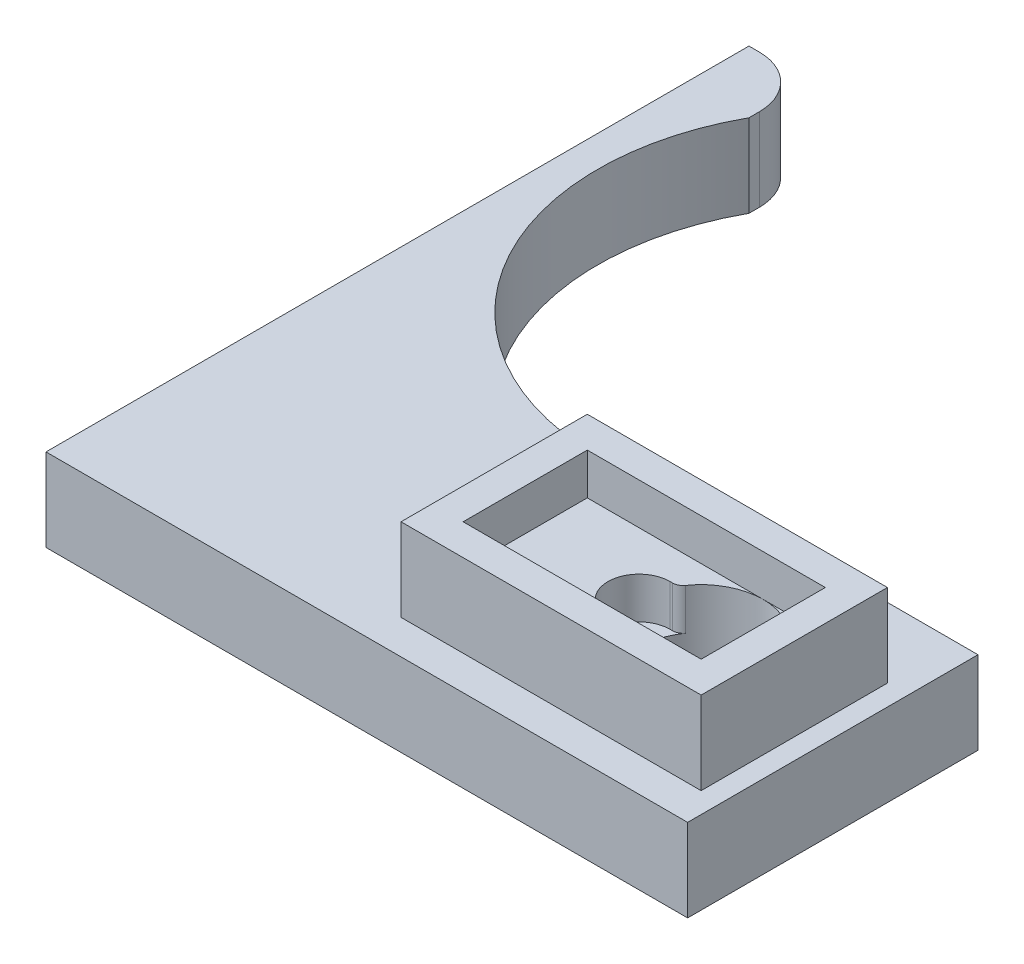
SolidWorks part; units mm, degrees
ref_plane "Plan de face" through (0, 0, 0) normal (0, 0, 1) x (1, 0, 0)
ref_plane "Plan de dessus" through (0, 0, 0) normal (0, 1, 0) x (1, 0, 0)
ref_plane "Plan de droite" through (0, 0, 0) normal (1, 0, 0) x (0, 0, -1)
sketch "Esquisse1" plane through (0, 0, 0) normal (0, 1, 0) x (1, 0, 0)
  line L1 (0, 0) -> (6, 0)
  line L2 (0, 0) -> (0, 67.9235)
  line L3 (0, 67.9235) -> (1, 67.9235)
  line L4 (6, 0) -> (6, 67.9235) construction
  line L5 (36, 0) -> (6, 0)
  line L6 (6, 61.9235) -> (6, 62.9235)
  line L7 (52, 50.3046) -> (52, 0) construction
  line L8 (36, 28.056) -> (62, 28.056)
  line L10 (36, 0) -> (62, 0)
  line L11 (62, 28.056) -> (62, 0)
  line L12 (36, 28.056) -> (36, 0) construction
  line L13 (52, 12.3046) -> (51, 12.3046) construction
  arc A0 (6, 61.9235) -> (36, 28.056) centre (27, 50.3046) ccw
  circle A1 centre (27, 50.3046) radius 25 construction
  arc A2 (1, 67.9235) -> (6, 62.9235) centre (1, 62.9235) cw
  circle A3 centre (51, 12.3046) radius 6
  dimension "D1" = 24
  dimension "D3" = 50
  dimension "D7" = 5
  dimension "D9" = 12
  dimension "D2" = 21
  dimension "D4" = 30
  dimension "D5" = 6
  dimension "D6" = 6
  dimension "D8" = 1
  dimension "D10" = 38
  dimension "D11" = 62
extrude "Boss.-Extru.1" add sketch "Esquisse1" along normal blind 8
sketch "Esquisse2" plane through (0, 8, 0) normal (0, 1, 0) x (1, 0, 0)
  line L0 (51, 12.3046) -> (45, 12.3046) construction
  line L1 (45, 15.3046) -> (45.2554, 15.3046)
  line L2 (45, 9.3046) -> (45.2554, 9.3046)
  line L8 (31, 21.3046) -> (60, 21.3046)
  line L9 (31, 21.3046) -> (31, 3.3046)
  line L10 (31, 3.3046) -> (60, 3.3046)
  line L11 (60, 21.3046) -> (60, 3.3046)
  circle A0 centre (51, 12.3046) radius 6 construction
  circle A1 centre (45, 12.3046) radius 3 construction
  arc A2 (46.0761, 15.7332) -> (46.0761, 8.876) centre (51, 12.3046) cw
  arc A3 (45, 15.3046) -> (45, 9.3046) centre (45, 12.3046) ccw
  arc A4 (45.2554, 9.3046) -> (46.0761, 8.876) centre (45.2554, 8.3046) cw
  arc A5 (45.2554, 15.3046) -> (46.0761, 15.7332) centre (45.2554, 16.3046) ccw
  point P15 (45.8038, 9.3046)
  point P18 (45.8038, 15.3046)
  point P27 (60, 12.3046)
  dimension "D1" = 12
  dimension "D2" = 6
  dimension "D4" = 1
  dimension "D3" = 6
  dimension "D5" = 9
  dimension "D7" = 18
  dimension "D8" = 29
extrude "Boss.-Extru.2" add sketch "Esquisse2" along normal blind 4 contours L9 L8 L11 L10 | A3 L2 A4 A2 A5 L1
sketch "Esquisse3" plane through (0, 12, 0) normal (0, 1, 0) x (1, 0, 0)
  line L1 (34, 18.3046) -> (57, 18.3046)
  line L2 (34, 18.3046) -> (34, 6.3046)
  line L3 (34, 6.3046) -> (57, 6.3046)
  line L4 (57, 18.3046) -> (57, 6.3046)
  line L5 (31, 21.3046) -> (60, 21.3046)
  line L6 (31, 21.3046) -> (31, 3.3046)
  line L7 (31, 3.3046) -> (60, 3.3046)
  line L8 (60, 21.3046) -> (60, 3.3046)
  arc A0 (46.0761, 8.876) -> (46.0761, 15.7332) centre (51, 12.3046) ccw construction
  dimension "D1" = 12
  dimension "D2" = 23
extrude "Boss.-Extru.3" add sketch "Esquisse3" along normal blind 4
sketch "Esquisse4" plane through (0, 0, 0) normal (0, -1, 0) x (1, 0, 0)
  line L0 (62, -28.056) -> (36, -28.056) construction
  line L1 (47.7, -17.056) -> (54.3, -17.056)
  line L3 (47.7, -28.056) -> (54.3, -28.056)
  line L5 (51, -12.3046) -> (51, -17.056) construction
  line L6 (51, -12.3046) -> (52.0099, -17.056) construction
  line L7 (55.1937, -16.1623) -> (57.7218, -28.056)
  line L8 (54.3, -17.056) -> (55.1937, -16.1623)
  line L9 (54.3, -28.056) -> (57.7218, -28.056)
  line L10 (54.3, -17.056) -> (54.3, -28.056) construction
  line L11 (46.8063, -16.1623) -> (44.2782, -28.056)
  line L12 (46.8063, -16.1623) -> (47.7, -17.056)
  line L13 (47.7, -17.056) -> (47.7, -28.056) construction
  line L14 (44.2782, -28.056) -> (47.7, -28.056)
  point P12 (51, -17.056)
  dimension "D1" = 12
  dimension "D2" = 3.3
  dimension "D3" = 6.6
  dimension "D4" = 11
  dimension "D5" = 135
extrude "Enlèv. mat.-Extru.1" cut sketch "Esquisse4" against normal blind 4
